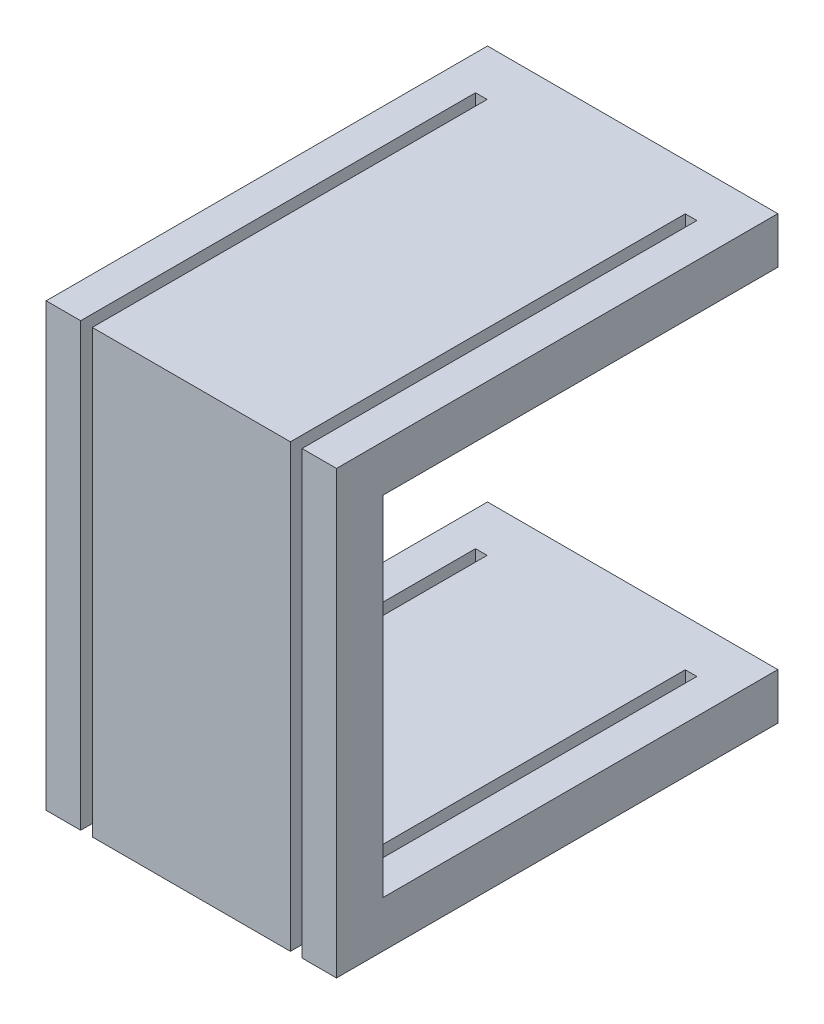
SolidWorks part; units mm, degrees
ref_plane "Front Plane" through (0, 0, 0) normal (0, 0, 1) x (1, 0, 0)
ref_plane "Top Plane" through (0, 0, 0) normal (0, 1, 0) x (1, 0, 0)
ref_plane "Right Plane" through (0, 0, 0) normal (1, 0, 0) x (0, 0, -1)
sketch "Sketch2" plane through (0, 0, 0) normal (1, 0, 0) x (0, 0, -1)
  line L1 (-2, 15) -> (2, 15)
  line L2 (-2, 15) -> (-2, -15)
  line L3 (-2, -15) -> (2, -15)
  line L4 (2, 15) -> (2, -15)
  line L5 (-2, 15) -> (2, -15) construction
  line L6 (-2, -15) -> (2, 15) construction
  line L7 (-2, -15) -> (36, -15)
  line L8 (-2, -15) -> (-2, -19)
  line L9 (-2, -19) -> (36, -19)
  line L10 (36, -15) -> (36, -19)
  line L11 (-2, 15) -> (36, 15)
  line L12 (-2, 15) -> (-2, 19)
  line L13 (-2, 19) -> (36, 19)
  line L14 (36, 15) -> (36, 19)
  point P0 (0, 0)
extrude "Boss-Extrude1" add sketch "Sketch2" along normal blind 25 contours L4 L1 L2 L3 | L11 L14 L13 L12 L1 | L10 L7 L3 L8 L9
sketch "Sketch3" plane through (0, 0, 2) normal (0, 0, 1) x (1, 0, 0)
  line L0 (0, 0) -> (2.9699, 0) construction
  line L1 (12.5, -19) -> (12.5, -8.2256) construction
  line L2 (25, -19) -> (0, -19) construction
  line L3 (25, 19) -> (0, 19) construction
  line L4 (2.9699, 19) -> (3.9699, 19)
  line L5 (2.9699, 19) -> (2.9699, -19)
  line L6 (2.9699, -19) -> (3.9699, -19)
  line L7 (3.9699, 19) -> (3.9699, -19)
  line L8 (21.0301, 19) -> (21.0301, -19)
  line L9 (22.0301, -19) -> (21.0301, -19)
  line L10 (22.0301, 19) -> (22.0301, -19)
  line L11 (22.0301, 19) -> (21.0301, 19)
extrude "Cut-Extrude1" cut sketch "Sketch3" against normal blind 34
